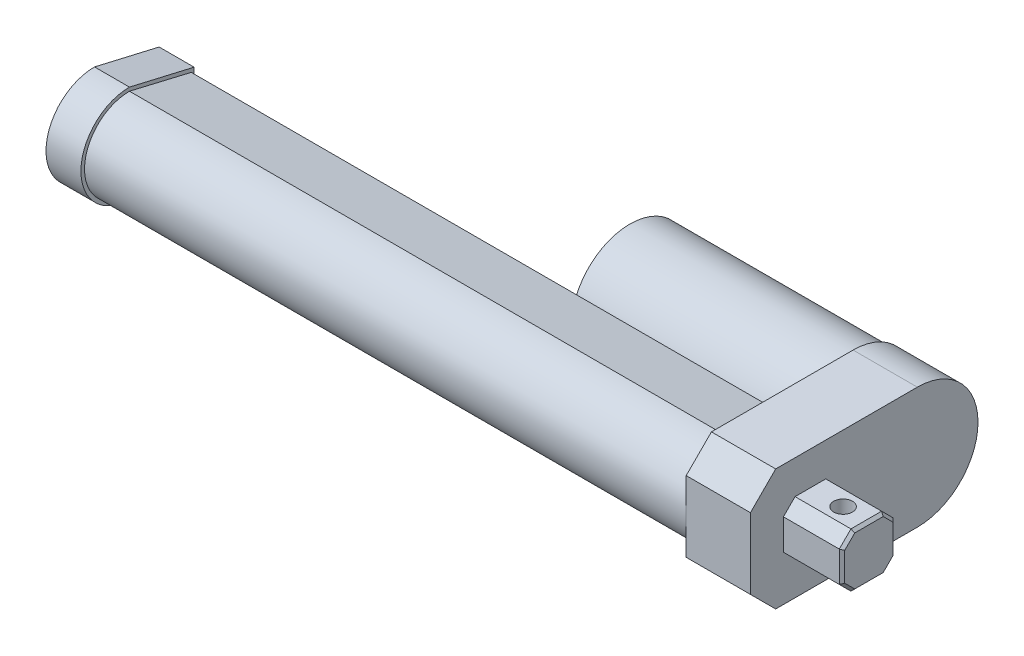
SolidWorks part; units mm, degrees
ref_plane "Front Plane" through (0, 0, 0) normal (0, 0, 1) x (1, 0, 0)
ref_plane "Top Plane" through (0, 0, 0) normal (0, 1, 0) x (1, 0, 0)
ref_plane "Right Plane" through (0, 0, 0) normal (1, 0, 0) x (0, 0, -1)
sketch "Sketch1" plane through (0, 0, 0) normal (1, 0, 0) x (0, 0, -1)
  line L1 (0, 0) -> (54.61, 0)
  line L2 (0, 0) -> (0, 39.6875)
  line L3 (0, 39.6875) -> (54.61, 39.6875)
  line L4 (54.61, 0) -> (54.61, 39.6875)
  arc A0 (54.61, 39.6875) -> (54.61, 0) centre (54.61, 19.8437) cw
  dimension "D1" = 39.6875
  dimension "D2" = 54.61
extrude "Boss-Extrude1" add sketch "Sketch1" along normal blind 21.0185 contours L1 L4 L3 L2 | A0 L4
chamfer "Chamfer1" distance 8.2618 2 edges at (10.5092, 0, 0) (10.5092, 39.6875, 0)
sketch "Sketch2" plane through (0, 0, 0) normal (-1, 0, 0) x (0, 0, 1)
  circle A0 centre (-54.61, 19.8437) radius 19.05
  dimension "D1" = 38.1
extrude "Boss-Extrude2" add sketch "Sketch2" along normal blind 73.025
sketch "Sketch3" plane through (-73.025, 0, 0) normal (-1, 0, 0) x (0, 0, 1)
  circle A0 centre (-54.61, 19.8437) radius 6.35
  dimension "D1" = 12.7
extrude "Boss-Extrude3" add sketch "Sketch3" along normal blind 2.54
sketch "Sketch4" plane through (0, 0, 0) normal (-1, 0, 0) x (0, 0, 1)
  line L0 (0, 19.8437) -> (-34.925, 19.8437)
  line L1 (0, 8.2618) -> (0, 31.4257) construction
  line L2 (-34.925, 9.906) -> (-34.925, 29.7815)
  line L4 (0, 19.8437) -> (-14.7066, 19.8437)
  line L5 (-34.925, 9.906) -> (-14.7066, 5.1371)
  line L6 (-34.925, 29.7815) -> (-14.7066, 34.5503)
  arc A0 (-14.7066, 5.1371) -> (-14.7066, 34.5503) centre (-14.7066, 19.8437) ccw
  point P6 (-34.925, 19.8437)
  point P11 (0, 19.8437)
  dimension "D5" = 14.7066
  dimension "D1" = 34.925
  dimension "D2" = 9.9377
  dimension "D4" = 14.7066
extrude "Boss-Extrude4" add sketch "Sketch4" along normal blind 196.85 contours L5 A0 L0 L2 | L0 A0 L6 L2
sketch "Sketch5" plane through (-196.85, 0, 0) normal (-1, 0, 0) x (0, 0, 1)
  line L0 (1.1681, 19.8437) -> (-35.8524, 19.8437)
  line L1 (-35.8524, 30.7975) -> (-35.8524, 8.89)
  line L2 (-35.8524, 8.89) -> (-14.7066, 3.969)
  line L3 (-14.7066, 35.7185) -> (-35.8524, 30.7975)
  arc A0 (-14.7066, 35.7185) -> (-14.7066, 3.969) centre (-14.7066, 19.8437) cw
  point P8 (-35.8524, 19.8437)
  line M1 (-34.925, 9.906) -> (-14.7066, 5.1371)
  arc M2 (-14.7066, 5.1371) -> (-14.7066, 34.5503) centre (-14.7066, 19.8437) ccw
  line M3 (-14.7066, 34.5503) -> (-34.925, 29.7815)
  line M4 (-34.925, 29.7815) -> (-34.925, 9.906)
  dimension "D1" = 15.8747
  dimension "D2" = 37.0205
  dimension "D3" = 10.9537
extrude "Boss-Extrude5" add sketch "Sketch5" along normal blind 11.43 contours L0 M2 M3 M4 | A0 L3 L1 L0 M4 M3 M2 | L0 M2 M4 M1 | A0 L0 L1 L2 M2 M1 M4
sketch "Sketch6" plane through (-208.28, 0, 0) normal (-1, 0, 0) x (0, 0, 1)
  circle A0 centre (-14.7066, 19.8437) radius 10.0012
  dimension "D1" = 20.0025
extrude "Cut-Extrude1" cut sketch "Sketch6" against normal blind 203.2
sketch "Sketch7" plane through (21.0185, 0, 0) normal (1, 0, 0) x (0, 0, -1)
  line L0 (0, 19.8437) -> (74.4538, 19.8437)
  line L1 (0, 8.2618) -> (0, 31.4257) construction
  line L2 (10.795, 28.6702) -> (10.795, 11.0172)
  line L3 (0, 19.8437) -> (10.795, 19.8437)
  line L5 (28.448, 11.0172) -> (10.795, 11.0172)
  line L6 (28.448, 11.0172) -> (28.448, 28.6702)
  line L7 (28.448, 28.6702) -> (10.795, 28.6702)
  arc A0 (54.61, 0) -> (54.61, 39.6875) centre (54.61, 19.8437) ccw construction
  point P10 (10.795, 19.8437)
  dimension "D1" = 10.795
extrude "Boss-Extrude6" add sketch "Sketch7" along normal blind 19.1643 contours L5 L6 L0 L2 | L6 L7 L2 L0
chamfer "Chamfer2" distance 3.81 4 edges at (30.6007, 28.6702, -10.795) (30.6007, 28.6702, -28.448) (30.6007, 11.0172, -28.448) (30.6007, 11.0172, -10.795)
sketch "Sketch8" plane through (0, 11.0172, 0) normal (0, -1, 0) x (1, 0, 0)
  line L0 (40.1828, -19.6215) -> (34.7853, -19.6215)
  line L1 (40.1828, -24.638) -> (40.1828, -14.605) construction
  line L2 (21.0185, -19.6215) -> (28.6385, -19.6215)
  line L3 (21.0185, -24.638) -> (21.0185, -14.605) construction
  line L4 (34.7853, -19.6215) -> (28.6385, -19.6215)
  circle A0 centre (31.7119, -19.6215) radius 3.0734
  dimension "D1" = 5.3975
  dimension "D2" = 7.62
extrude "Cut-Extrude2" cut sketch "Sketch8" against normal up to surface (17.653 mm away) contours L4 A0 | L4 A0 up to face at (30.6007, 28.6702, -19.6215)
chamfer "Chamfer3" distance 0.889 8 edges at (40.1828, 12.9223, -12.7) (40.1828, 19.8438, -10.795) (40.1828, 26.7652, -12.7) (40.1828, 28.6702, -19.6215) (40.1828, 26.7652, -26.543) (40.1828, 19.8437, -28.448) (40.1828, 12.9223, -26.543) (40.1828, 11.0172, -19.6215)
